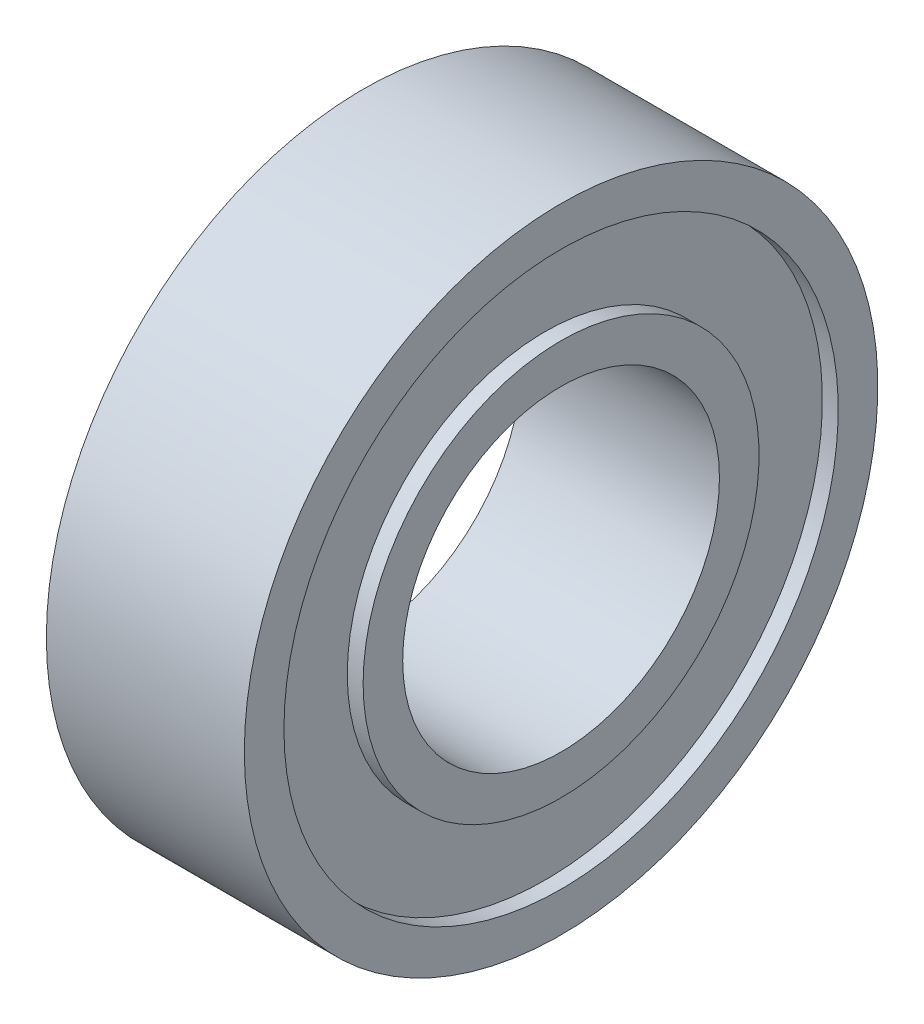
SolidWorks part; units mm, degrees
material "Plain Carbon Steel"
ref_plane "Front Plane" through (0, 0, 0) normal (0, 0, 1) x (1, 0, 0)
ref_plane "Top Plane" through (0, 0, 0) normal (0, 1, 0) x (1, 0, 0)
ref_plane "Right Plane" through (0, 0, 0) normal (1, 0, 0) x (0, 0, -1)
sketch "Sketch1" plane through (0, 0, 0) normal (0, 0, 1) x (1, 0, 0)
  line L0 (-2.5, 0) -> (2.5, 0) construction
  line L1 (-2.5, 8) -> (2.5, 8)
  line L2 (-2.5, 8) -> (-2.5, 7)
  line L3 (-2.5, 4) -> (2.5, 4)
  line L4 (2.5, 8) -> (2.5, 7)
  line L5 (2.5, 0) -> (2.5, 4) construction
  line L6 (-2.5, 0) -> (-2.5, 4) construction
  line L7 (0, 0) -> (0, 8) construction
  line L8 (-2.5, 5) -> (-2.5, 4)
  line L9 (-2.5, 5) -> (-2.1, 5)
  line L10 (2.5, 5) -> (2.5, 4)
  line L11 (-2.5, 7) -> (-2.1, 7)
  line L12 (-2.1, 5) -> (-2.1, 7)
  line L13 (2.5, 7) -> (2.1, 7)
  line L15 (2.5, 5) -> (2.1, 5)
  line L16 (2.1, 7) -> (2.1, 5)
  dimension "D1" = 16
  dimension "D2" = 5
  dimension "D3" = 8
  dimension "D4" = 0.4
  dimension "D5" = 10
  dimension "D6" = 14
revolve "Revolve1" add sketch "Sketch1" angle 360 about L0
